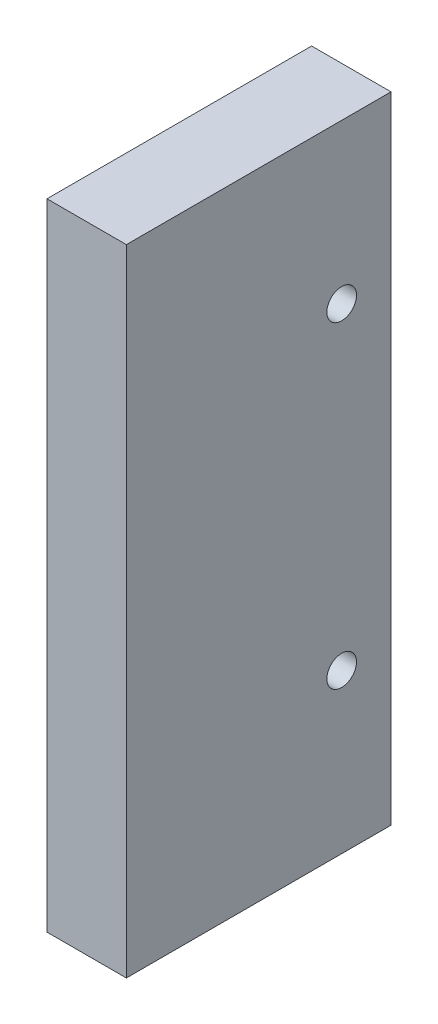
SolidWorks part; units mm, degrees
ref_plane "Front Plane" through (0, 0, 0) normal (0, 0, 1) x (1, 0, 0)
ref_plane "Top Plane" through (0, 0, 0) normal (0, 1, 0) x (1, 0, 0)
ref_plane "Right Plane" through (0, 0, 0) normal (1, 0, 0) x (0, 0, -1)
sketch "Sketch1" plane through (0, 0, 0) normal (0, 0, 1) x (1, 0, 0)
  line L1 (0, 0) -> (9.525, 0)
  line L2 (0, 0) -> (0, 76.2)
  line L3 (0, 76.2) -> (9.525, 76.2)
  line L4 (9.525, 0) -> (9.525, 76.2)
  dimension "D1" = 9.525
  dimension "D2" = 76.2
extrude "Boss-Extrude1" add sketch "Sketch1" along normal blind 31.75
sketch "Sketch2" plane through (0, 0, 0) normal (-1, 0, 0) x (0, 0, 1)
  line L0 (5.9182, 76.2) -> (5.9182, 0) construction
  line L1 (31.75, 76.2) -> (0, 76.2) construction
  line L2 (31.75, 0) -> (0, 0) construction
  line L3 (0, 76.2) -> (0, 0) construction
  circle A0 centre (5.9182, 57.15) radius 1.778
  circle A1 centre (5.9182, 19.05) radius 1.778
  dimension "D2" = 3.556
  dimension "D3" = 19.05
  dimension "D1" = 5.9182
  dimension "D4" = 38.1
extrude "Cut-Extrude1" cut sketch "Sketch2" against normal through all
sketch "Sketch3" plane through (0, 0, 0) normal (0, -1, 0) x (1, 0, 0)
  line L0 (4.7625, 31.75) -> (4.7625, 0) construction
  line L1 (0, 31.75) -> (9.525, 31.75) construction
  line L2 (0, 0) -> (9.525, 0) construction
  circle A0 centre (4.7625, 25.4) radius 1.7272
  circle A1 centre (4.7625, 12.7) radius 1.7272
  dimension "D2" = 3.4544
  dimension "D3" = 6.35
  dimension "D1" = 12.7
extrude "Cut-Extrude2" cut sketch "Sketch3" against normal blind 19.05
